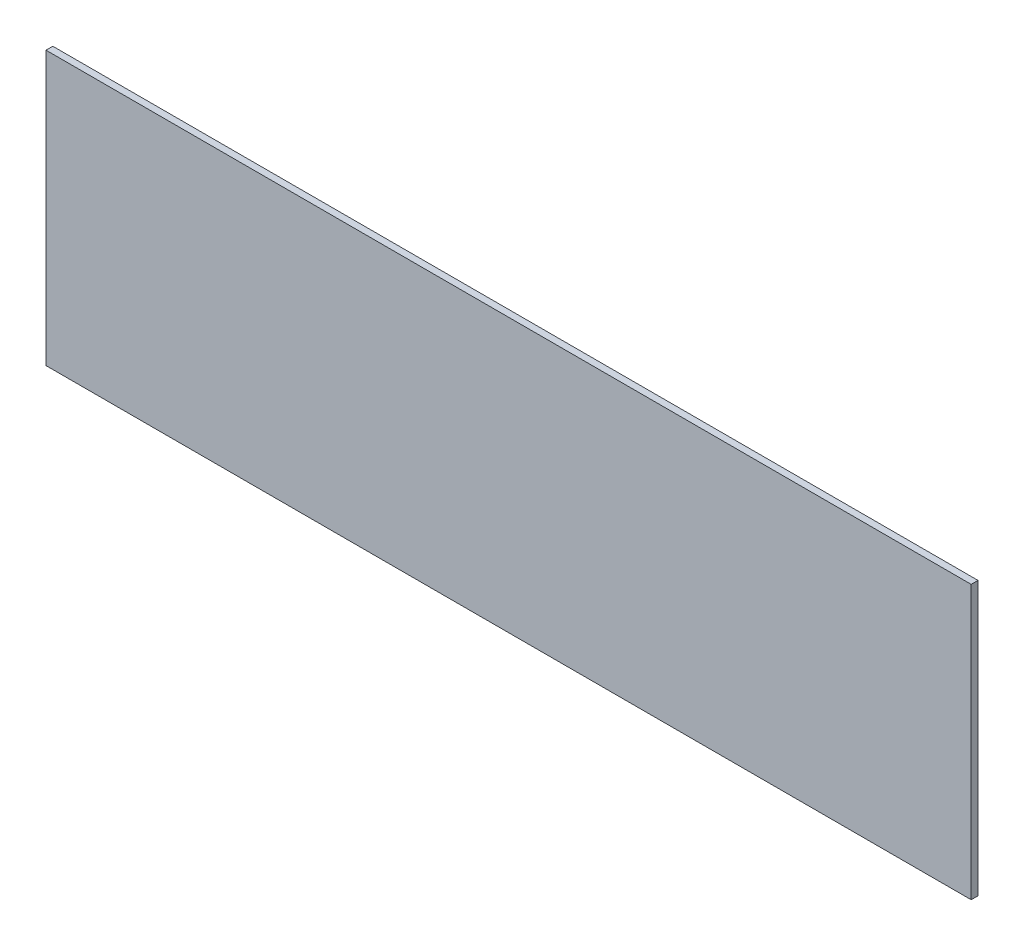
SolidWorks part; units mm, degrees
ref_plane "Front Plane" through (0, 0, 0) normal (0, 0, 1) x (1, 0, 0)
ref_plane "Top Plane" through (0, 0, 0) normal (0, 1, 0) x (1, 0, 0)
ref_plane "Right Plane" through (0, 0, 0) normal (1, 0, 0) x (0, 0, -1)
sketch "Sketch1" plane through (0, 0, 0) normal (0, 0, 1) x (1, 0, 0)
  line L1 (101.6, -30) -> (-101.6, -30)
  line L2 (101.6, -30) -> (101.6, 30)
  line L3 (101.6, 30) -> (-101.6, 30)
  line L4 (-101.6, -30) -> (-101.6, 30)
  line L5 (101.6, -30) -> (-101.6, 30) construction
  line L6 (101.6, 30) -> (-101.6, -30) construction
  point P0 (0, 0)
extrude "Boss-Extrude1" add sketch "Sketch1" along normal blind 1.5 contours L4 L3 L2 L1
